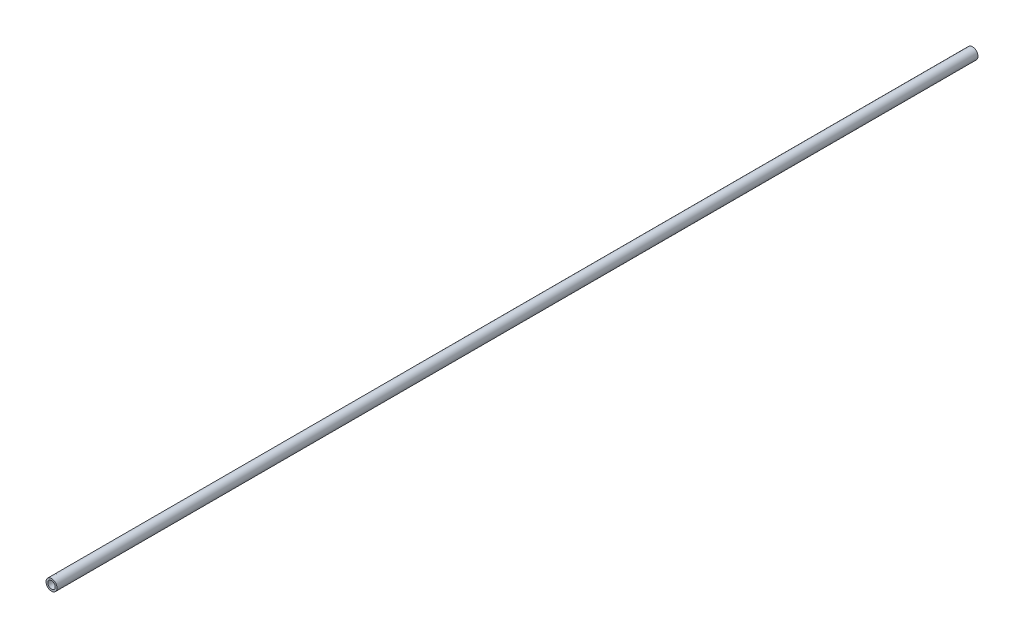
SolidWorks part; units mm, degrees
material "Poltrusion Carbon Fiber"
ref_plane "Front Plane" through (0, 0, 0) normal (0, 0, 1) x (1, 0, 0)
ref_plane "Top Plane" through (0, 0, 0) normal (0, 1, 0) x (1, 0, 0)
ref_plane "Right Plane" through (0, 0, 0) normal (1, 0, 0) x (0, 0, -1)
sketch "Эскиз1" plane through (0, 0, 0) normal (0, 0, 1) x (1, 0, 0)
  circle A0 centre (0, 0) radius 3
  circle A1 centre (0, 0) radius 2
  dimension "D1" = 6
  dimension "D2" = 4
extrude "Бобышка-Вытянуть1" add sketch "Эскиз1" along normal mid plane 500
